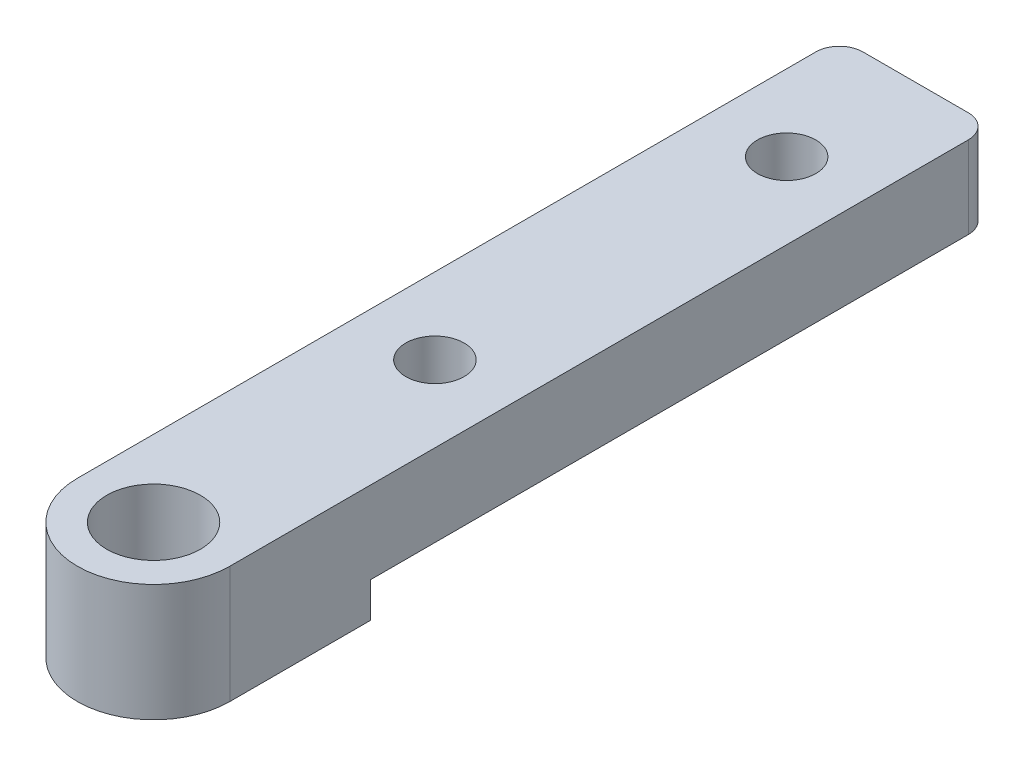
SolidWorks part; units mm, degrees
material "6061-T6 (SS)"
ref_plane "Front Plane" through (0, 0, 0) normal (0, 0, 1) x (1, 0, 0)
ref_plane "Top Plane" through (0, 0, 0) normal (0, 1, 0) x (1, 0, 0)
ref_plane "Right Plane" through (0, 0, 0) normal (1, 0, 0) x (0, 0, -1)
sketch "Sketch1" plane through (0, 0, 0) normal (0, 1, 0) x (1, 0, 0)
  line L0 (-6.5, 0) -> (-6.5, 65)
  line L1 (-6.5, 65) -> (6.5, 65)
  line L2 (6.5, 65) -> (6.5, 0)
  line L3 (0, 54) -> (0, 24) construction
  line L4 (-6.5, 12) -> (6.5, 12) construction
  line L5 (-6.5, 65) -> (6.5, 12) construction
  arc A0 (-6.5, 0) -> (6.5, 0) centre (0, 0) ccw
  circle A1 centre (0, 0) radius 3.9942
  dimension "D1" = 13
  dimension "D2" = 7.9883
  dimension "D3" = 13
  dimension "D4" = 65
  dimension "D5" = 12
  dimension "D6" = 30
  dimension "D7" = 12
extrude "Boss-Extrude1" add sketch "Sketch1" along normal blind 10
sketch "Sketch2" plane through (0, 0, 0) normal (0, -1, 0) x (1, 0, 0)
  line L1 (-6.5, -65) -> (6.5, -65)
  line L2 (-6.5, -65) -> (-6.5, -12)
  line L3 (-6.5, -12) -> (6.5, -12)
  line L4 (6.5, -65) -> (6.5, -12)
extrude "Cut-Extrude1" cut sketch "Sketch2" against normal blind 3
hole_wizard "#10 Clearance Hole1" positions "Sketch4" profile "Sketch3" hole size "#10" standard "Ansi Inch"
sketch "Sketch4" plane through (0, 3, 0) normal (0, -1, 0) x (1, 0, 0)
  point P0 (0, -54)
  point P1 (0, -24)
sketch "Sketch3" plane through (0, 3, -54) normal (1, 0, 0) x (0, 0, -1)
  line L0 (0, 0) -> (0, 41.4957)
  line L1 (0, 41.4957) -> (2.4892, 40)
  line L2 (2.4892, 40) -> (2.4892, 0)
  line L5 (2.4892, 0) -> (0, 0)
  line L10 (0, 41.4957) -> (-2.4892, 40) construction
  line L11 (0, -6.35) -> (0, 107.95) construction
  dimension "Hole Dia." = 4.9784
  dimension "Hole Depth" = 40
  dimension "Drill Angle" = 118
fillet "Fillet1" radius 2 2 edges at (-6.5, 6.5, -65) (6.5, 6.5, -65)
